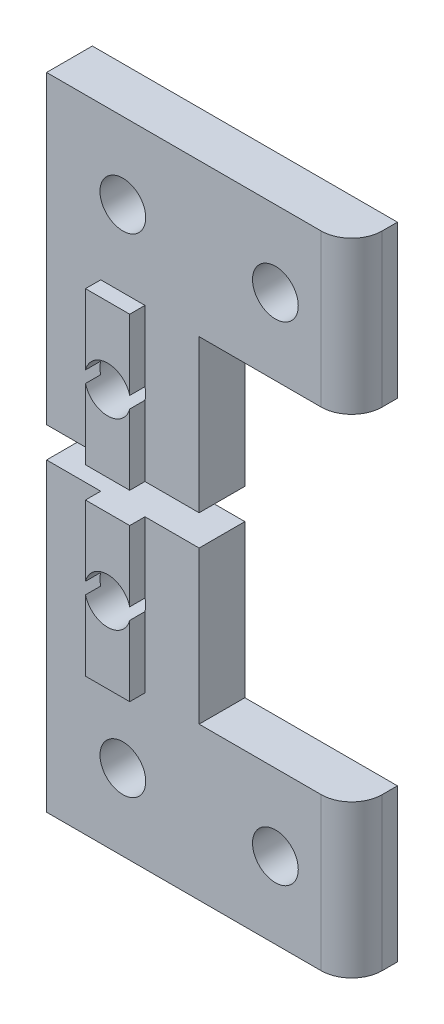
SolidWorks part; units mm, degrees
ref_plane "Front Plane" through (0, 0, 0) normal (0, 0, 1) x (1, 0, 0)
ref_plane "Top Plane" through (0, 0, 0) normal (0, 1, 0) x (1, 0, 0)
ref_plane "Right Plane" through (0, 0, 0) normal (1, 0, 0) x (0, 0, -1)
sketch "Esquisse1" plane through (0, 0, 0) normal (0, 0, 1) x (1, 0, 0)
  line L0 (0, 0) -> (20, 0)
  line L1 (20, 0) -> (20, 10)
  line L2 (20, 10) -> (10, 10)
  line L3 (10, 10) -> (10, 20)
  line L4 (10, 20) -> (0, 20)
  line L5 (0, 20) -> (0, 0)
  dimension "D1" = 10
  dimension "D3" = 20
extrude "Boss.-Extru.1" add sketch "Esquisse1" along normal blind 3
sketch "Esquisse2" plane through (0, 0, 3) normal (0, 0, 1) x (1, 0, 0)
  line L0 (10, 20) -> (0, 20) construction
  line L1 (3.55, 20) -> (6.45, 20)
  line L2 (3.55, 20) -> (3.55, 10)
  line L3 (3.55, 10) -> (6.45, 10)
  line L4 (6.45, 20) -> (6.45, 10)
  line L5 (20, 10) -> (10, 10) construction
  point P4 (5, 20)
  point P7 (5, 20)
  dimension "D1" = 2.9
extrude "Boss.-Extru.2" add sketch "Esquisse2" along normal blind 1
sketch "Esquisse4" plane through (0, 0, 4) normal (0, 0, 1) x (1, 0, 0)
  line L0 (10, 20) -> (0, 20) construction
  line L1 (20, 0) -> (20, 10) construction
  circle A0 centre (5, 15) radius 1.5
  circle A1 centre (5, 5) radius 1.5
  circle A2 centre (15, 5) radius 1.5
  point P9 (5, 20)
  point P12 (20, 5)
  dimension "D3" = 3
  dimension "D1" = 5
  dimension "D2" = 5
extrude "Enlèv. mat.-Extru.2" cut sketch "Esquisse4" against normal through all
fillet "Congé1" radius 2 1 edges at (20, 5, 3)
ref_plane "Plan1" through (0, 21, 0) normal (0, 1, 0) x (1, 0, 0)
mirror "Symétrie2" about plane through (0, 21, 0) normal (0, 1, 0) of bodies 104
